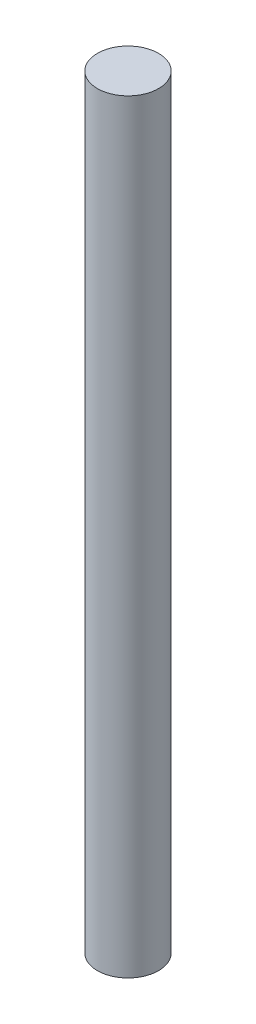
SolidWorks part; units mm, degrees
ref_plane "前视基准面" through (0, 0, 0) normal (0, 0, 1) x (1, 0, 0)
ref_plane "上视基准面" through (0, 0, 0) normal (0, 1, 0) x (1, 0, 0)
ref_plane "右视基准面" through (0, 0, 0) normal (1, 0, 0) x (0, 0, -1)
sketch "草图1" plane through (0, 0, 0) normal (0, 1, 0) x (1, 0, 0)
  circle A0 centre (0, 0) radius 4
  dimension "D1" = 8
extrude "凸台-拉伸1" add sketch "草图1" along normal blind 100
